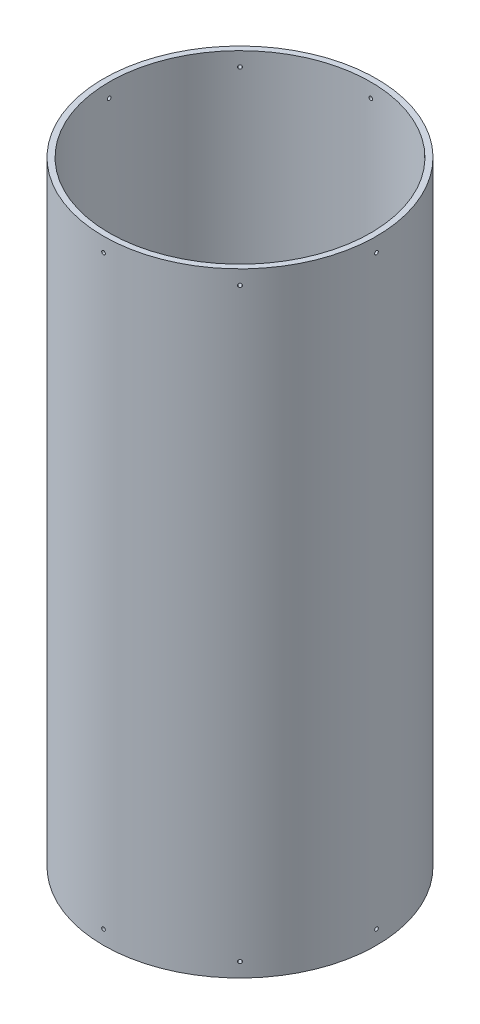
SolidWorks part; units mm, degrees
material "6061-T6"
ref_plane "Front Plane" through (0, 0, 0) normal (0, 0, 1) x (1, 0, 0)
ref_plane "Top Plane" through (0, 0, 0) normal (0, 1, 0) x (1, 0, 0)
ref_plane "Right Plane" through (0, 0, 0) normal (1, 0, 0) x (0, 0, -1)
sketch "Sketch1" plane through (0, 0, 0) normal (0, 1, 0) x (1, 0, 0)
  circle A0 centre (0, 0) radius 146.05
  circle A1 centre (0, 0) radius 152.4
  dimension "D1" = 292.1
  dimension "D2" = 304.8
extrude "Boss-Extrude1" add sketch "Sketch1" along normal blind 685.8
ref_plane "Plane1" through (0, 0, 152.4) normal (0, 0, 1) x (1, 0, 0)
ref_plane "Plane2" through (-152.4, 0, 0) normal (-1, 0, 0) x (0, 0, 1)
hole_wizard "#10-32 Tapped Hole1" positions "Sketch2" profile "Sketch3" tap size "#10-32" standard "ANSI Inch"
sketch "Sketch2" plane through (0, 0, 152.4) normal (0, 0, 1) x (1, 0, 0)
  line L0 (0, 669.925) -> (0, 15.875)
  line L1 (0, 15.875) -> (0, 0)
  line L3 (152.4, 685.8) -> (-152.4, 685.8) construction
  line L4 (-152.4, 0) -> (152.4, 0) construction
  point P0 (0, 669.925)
  point P2 (0, 15.875)
  dimension "D1" = 15.875
  dimension "D2" = 15.875
sketch "Sketch3" plane through (0, 669.925, 152.4) normal (1, 0, 0) x (0, -1, 0)
  line L0 (0, 0) -> (0, 13.1513)
  line L1 (0, 13.1513) -> (2.0193, 11.938)
  line L2 (2.0193, 11.938) -> (2.0193, 0)
  line L5 (2.0193, 0) -> (0, 0)
  line L10 (0, 13.1513) -> (-2.0193, 11.938) construction
  line L11 (0, -6.35) -> (0, 107.95) construction
  dimension "Tap Drill Dia." = 4.0386
  dimension "Tap Drill Depth" = 11.938
  dimension "Drill Angle" = 118
cosmetic thread "Hole Thread1" parameters "D1"=9.652, "D2"=4.826
cosmetic thread "Hole Thread2" parameters "D1"=9.652, "D2"=4.826
pattern_circular "CirPattern1" count 8 over 360 about axis through (0, 0, 0) along (0, 1, 0) of "#10-32 Tapped Hole1"
hole_wizard "Hole1" positions "Sketch4" profile "Sketch6" legacy
sketch "Sketch4" plane through (-152.4, 0, 0) normal (1, 0, 0) x (0, 0, -1)
  line L0 (0, 104.775) -> (0, 0)
  point P0 (0, 104.775)
  dimension "D1" = 104.775
sketch "Sketch6" plane through (-152.4, 104.775, 0) normal (0, 1, 0) x (0, 0, 1)
  line L0 (0, 0) -> (0, 6.35)
  line L1 (0, 6.35) -> (22.225, 6.35)
  line L2 (22.225, 6.35) -> (22.225, 0)
  line L3 (22.225, 0) -> (0, 0)
  line L4 (0, 110) -> (0, -10) construction
  dimension "Diameter" = 44.45
  dimension "Depth" = 6.35
